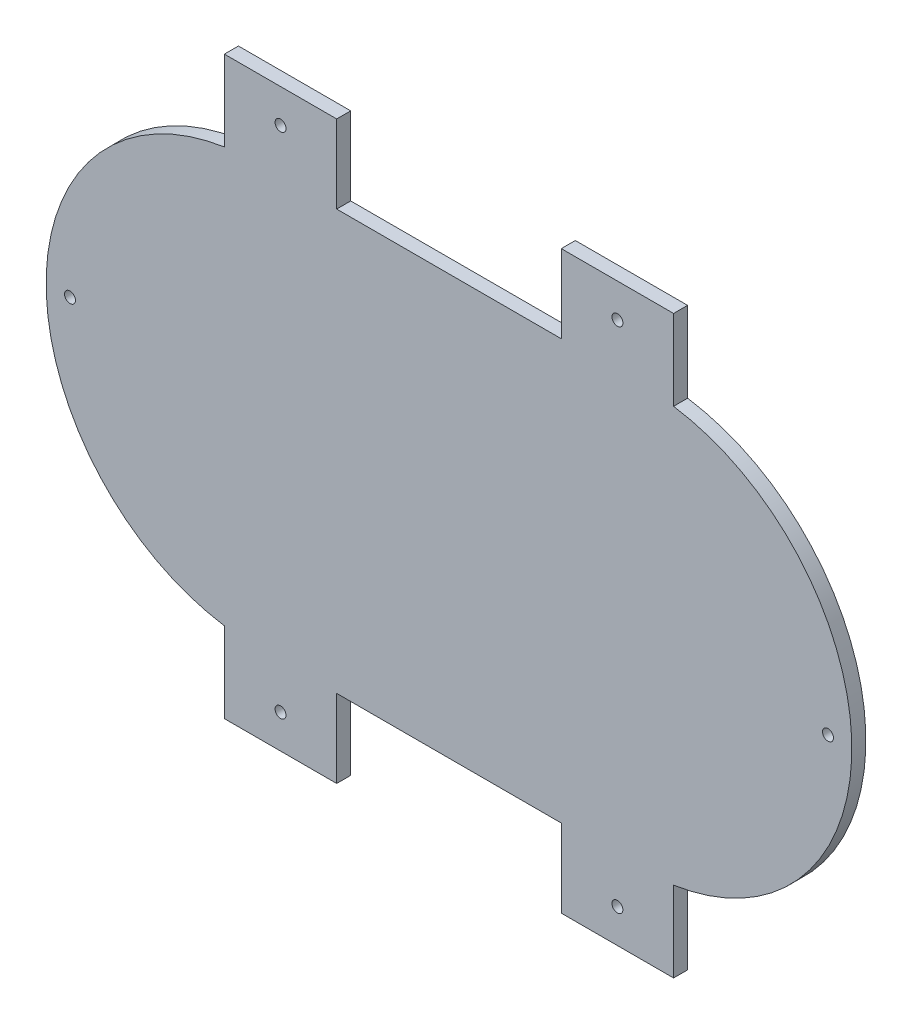
SolidWorks part; units mm, degrees
ref_plane "Front Plane" through (0, 0, 0) normal (0, 0, 1) x (1, 0, 0)
ref_plane "Top Plane" through (0, 0, 0) normal (0, 1, 0) x (1, 0, 0)
ref_plane "Right Plane" through (0, 0, 0) normal (1, 0, 0) x (0, 0, -1)
sketch "Sketch1" plane through (0, 0, 0) normal (0, 0, 1) x (1, 0, 0)
  line L0 (24.7012, -18.0878) -> (162.3012, -18.0878) construction
  line L18 (24.7012, 36.6122) -> (162.3012, 36.6122)
  line L19 (24.7012, -72.7878) -> (162.3012, -72.7878)
  line L20 (24.7012, 56.6122) -> (162.3012, 56.6122)
  line L21 (24.7012, -92.7878) -> (162.3012, -92.7878)
  line L34 (13.5012, -91.9434) -> (13.5012, -113.2964)
  line L35 (53.5012, -120.5878) -> (13.5012, -120.5878)
  line L36 (53.5012, -92.7878) -> (53.5012, -120.5878)
  line L37 (13.5012, -113.2964) -> (13.5012, -120.5878)
  line L38 (133.5012, -92.7878) -> (133.5012, -120.5878)
  line L39 (133.5012, -120.5878) -> (173.5012, -120.5878)
  line L40 (173.5012, -120.5878) -> (173.5012, -91.9434)
  line L41 (53.5012, 56.6122) -> (53.5012, 84.4122)
  line L42 (53.5012, 84.4122) -> (13.5012, 84.4122)
  line L43 (13.5012, 84.4122) -> (13.5012, 55.7678)
  line L44 (133.5012, 56.6122) -> (133.5012, 84.4122)
  line L45 (133.5012, 84.4122) -> (173.5012, 84.4122)
  line L46 (173.5012, 84.4122) -> (173.5012, 55.7678)
  line L47 (13.5012, 64.4122) -> (53.5012, 64.4122)
  line L48 (133.5012, 64.4122) -> (173.5012, 64.4122)
  line L49 (13.5012, -100.5878) -> (53.5012, -100.5878)
  line L50 (133.5012, -100.5878) -> (173.5012, -100.5878)
  line L51 (53.5012, 56.6122) -> (53.5012, 53.6122)
  line L52 (53.5012, 53.6122) -> (13.5012, 53.6122)
  line L53 (13.5012, 53.6122) -> (13.5012, 55.7678)
  line L54 (133.5012, 56.6122) -> (133.5012, 53.6122)
  line L55 (133.5012, 53.6122) -> (173.5012, 53.6122)
  line L56 (173.5012, 53.6122) -> (173.5012, 55.7678)
  line L57 (53.5012, -92.7878) -> (53.5012, -89.7878)
  line L58 (53.5012, -89.7878) -> (13.5012, -89.7878)
  line L59 (13.5012, -89.7878) -> (13.5012, -91.9434)
  line L60 (133.5012, -92.7878) -> (133.5012, -89.7878)
  line L61 (133.5012, -89.7878) -> (173.5012, -89.7878)
  line L62 (173.5012, -89.7878) -> (173.5012, -91.9434)
  arc A8 (24.7012, 36.6122) -> (24.7012, -72.7878) centre (24.7012, -18.0878) ccw
  arc A9 (162.3012, -72.7878) -> (162.3012, 36.6122) centre (162.3012, -18.0878) ccw
  arc A10 (162.3012, -92.7878) -> (162.3012, 56.6122) centre (162.3012, -18.0878) ccw
  arc A11 (24.7012, 56.6122) -> (24.7012, -92.7878) centre (24.7012, -18.0878) ccw
  circle A12 centre (33.5012, 72.4122) radius 1.95
  circle A13 centre (153.5012, 72.4122) radius 1.95
  circle A14 centre (33.5012, -108.5878) radius 1.95
  circle A15 centre (153.5012, -108.5878) radius 1.95
  circle A16 centre (228.5012, -18.0878) radius 1.95
  circle A17 centre (-41.4988, -18.0878) radius 1.95
  point P2 (93.5012, -18.0878)
  point P7 (-29.9988, -18.0878)
  point P8 (217.0012, -18.0878)
  point P15 (93.5012, 36.6122)
  point P16 (93.5012, 56.6122)
  point P17 (133.5012, 56.6122)
  point P18 (173.5012, 56.6122)
  point P19 (173.5012, 55.7678)
  point P20 (53.5012, 56.6122)
  point P21 (53.5012, 36.6122)
  point P22 (93.5012, -72.7878)
  point P23 (93.5012, -92.7878)
  point P24 (59.5116, -72.7878)
  point P25 (53.5012, -92.7878)
  point P26 (40.8007, -72.7878)
  point P27 (13.5012, -92.7878)
  point P28 (116.4883, -72.7878)
  point P29 (133.5012, -92.7878)
  point P30 (136.0432, -72.7878)
  point P31 (173.5012, -92.7878)
  point P32 (13.5012, 56.6122)
  point P33 (38.2497, 36.6122)
  point P34 (13.5012, -91.9434)
  point P35 (173.5012, -91.9434)
  point P36 (13.5012, 55.7678)
  point P62 (13.5012, 64.4122)
  point P63 (53.5012, 64.4122)
  point P68 (133.5012, 64.4122)
  point P69 (173.5012, 64.4122)
  point P71 (-49.9988, -18.0878)
  point P74 (53.5012, -100.5878)
  point P75 (13.5012, -100.5878)
  point P80 (133.5012, -100.5878)
  point P81 (173.5012, -100.5878)
  point P87 (237.0012, -18.0878)
  dimension "D1" = 54.7
  dimension "D15" = 3.9
  dimension "D18" = 3.9
  dimension "D22" = 3.9
  dimension "D27" = 3.9
  dimension "D41" = 3.9
  dimension "D43" = 3.9
  dimension "D2" = 40
  dimension "D3" = 40
  dimension "D4" = 40
  dimension "D5" = 40
  dimension "D6" = 40
  dimension "D7" = 40
  dimension "D8" = 40
  dimension "D9" = 40
  dimension "D10" = 27.8
  dimension "D11" = 27.8
  dimension "D12" = 27.8
  dimension "D13" = 20
  dimension "D14" = 20
  dimension "D16" = 8
  dimension "D17" = 20
  dimension "D19" = 20
  dimension "D20" = 20
  dimension "D21" = 20
  dimension "D23" = 8
  dimension "D24" = 20
  dimension "D25" = 20
  dimension "D26" = 20
  dimension "D28" = 20
  dimension "D29" = 3
  dimension "D30" = 3
  dimension "D31" = 27.8
  dimension "D32" = 20
  dimension "D33" = 20
  dimension "D34" = 8
  dimension "D35" = 40
  dimension "D36" = 40
  dimension "D37" = 40
  dimension "D38" = 27.8
  dimension "D39" = 8
  dimension "D40" = 40
  dimension "D42" = 8.5
  dimension "D44" = 8.5
extrude "Boss-Extrude1" add sketch "Sketch1" along normal mid plane 5
